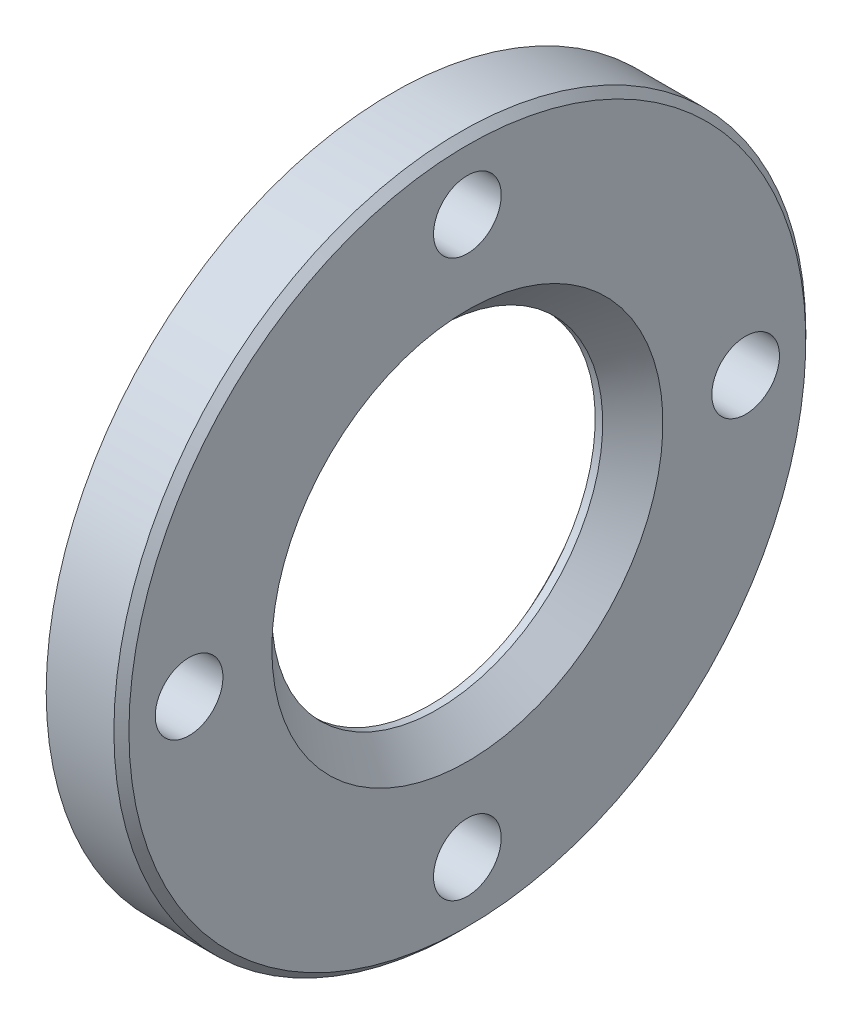
SolidWorks part; units mm, degrees
material "Сплав 3М ОСТ 1.92077-91"
ref_plane "Plane1" through (0, 0, 0) normal (0, 0, 1) x (1, 0, 0)
ref_plane "Plane2" through (0, 0, 0) normal (0, 1, 0) x (1, 0, 0)
ref_plane "Plane3" through (0, 0, 0) normal (1, 0, 0) x (0, 0, -1)
sketch "Эскиз1" plane through (0, 0, 0) normal (0, 0, 1) x (1, 0, 0)
  line L0 (0, 0) -> (52.6294, 0) construction
  line L1 (0, 23) -> (0, 14.5)
  line L2 (0, 14.5) -> (2.5, 14.5)
  line L3 (2.5, 14.5) -> (2.5, 11)
  line L4 (2.5, 11) -> (3, 11)
  line L5 (3, 11) -> (5, 13)
  line L6 (5, 13) -> (5, 23)
  line L7 (5, 23) -> (0, 23)
  dimension "D1" = 45
  dimension "D2" = 2.5
  dimension "D3" = 0.5
  dimension "D4" = 5
  dimension "D5" = 29
  dimension "D6" = 22
  dimension "D7" = 46
revolve "Повернуть1" add sketch "Эскиз1" angle 360 about L0
sketch "Эскиз2" plane through (5, 0, 0) normal (1, 0, 0) x (0, 0, -1)
  circle A0 centre (0, 18.5) radius 2.25
  dimension "D1" = 4.5
  dimension "D2" = 18.5
extrude "Вырез-Вытянуть1" cut sketch "Эскиз2" against normal through all
sketch "Sketch2" [suppressed] plane through (5, 13.8752, 3.6628) normal (-1, 0, 0) x (0, 0, 1)
  line L1 (-13.631, 9.0516) -> (4.9828, 17.1446) construction
  line L2 (-13.631, 9.0516) -> (-24.6964, 4.2406)
  line L3 (-13.631, 9.0516) -> (-23.8304, 32.5101)
  line L4 (-13.631, 9.0516) -> (-3.6628, -13.8752) construction
  line L5 (-3.6628, -13.8752) -> (-3.6628, 10.1248) construction
  point P0 (-13.631, 9.0516)
  dimension "D1" = 90
  dimension "D3" = 25
  dimension "D4" = 23.499
ref_plane "Plane4444" [suppressed] through (-10, 9.1707, -3.9873) normal (-0.7071, 0.6485, -0.2819) x (-0.7063, -0.6287, 0.3254)
sketch "Sketch3" [suppressed] plane through (-10, 9.1707, -3.9873) normal (-0.7071, 0.6485, -0.2819) x (-0.7063, -0.6287, 0.3254)
  circle A0 centre (-21.189, 1.0134) radius 0.75
extrude "Cut-Extrude1" [suppressed] cut sketch "Sketch3" against normal through all and the other way through all
other "Сверление косое под проволоку<1>" [suppressed]
pattern_circular "Круговой массив1" count 4 over 360 about axis through (0, 0, 0) along (1, 0, 0) of "Вырез-Вытянуть1", "Cut-Extrude1"
chamfer "Фаска1" distance 0.5 angle 45 1 edges at (5, 0, 23)
